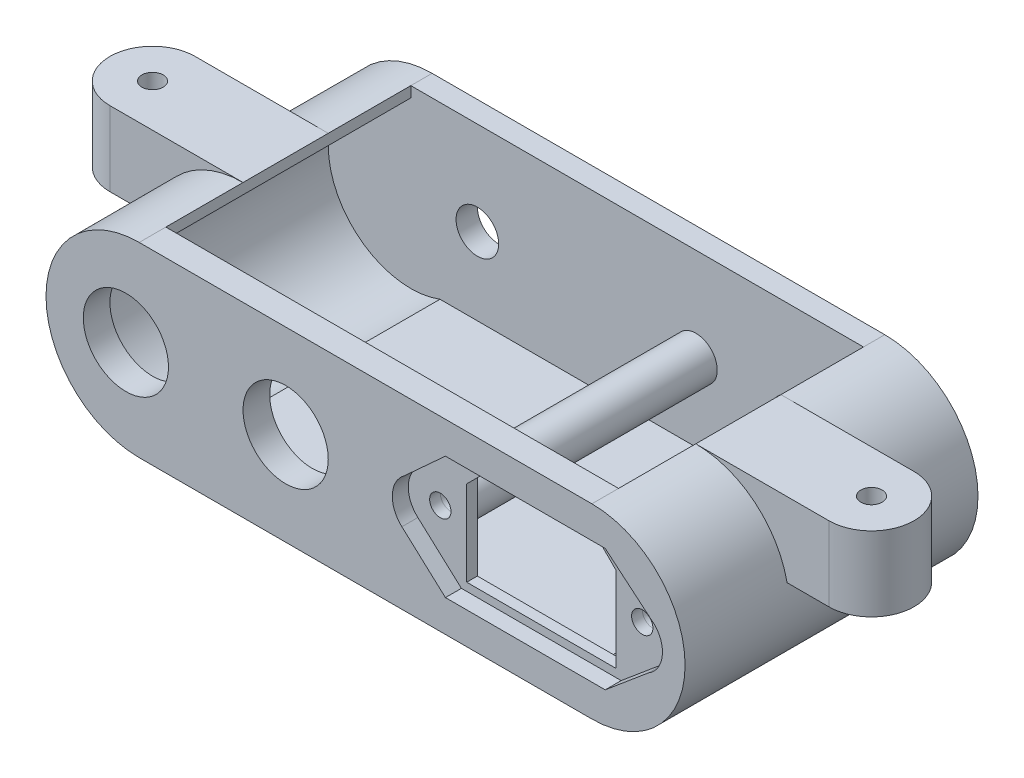
SolidWorks part; units mm, degrees
ref_plane "Front Plane" through (0, 0, 0) normal (0, 0, 1) x (1, 0, 0)
ref_plane "Top Plane" through (0, 0, 0) normal (0, 1, 0) x (1, 0, 0)
ref_plane "Right Plane" through (0, 0, 0) normal (1, 0, 0) x (0, 0, -1)
sketch "Sketch1" plane through (0, 0, 0) normal (0, 0, 1) x (1, 0, 0)
  line L1 (-60, 17.5) -> (60, 17.5)
  line L2 (-60, 17.5) -> (-60, -17.5)
  line L3 (-60, -17.5) -> (60, -17.5)
  line L4 (60, 17.5) -> (60, -17.5)
  line L5 (-60, 17.5) -> (60, -17.5) construction
  line L6 (-60, -17.5) -> (60, 17.5) construction
  point P0 (0, 0)
  dimension "D1" = 120
  dimension "D2" = 35
extrude "Boss-Extrude1" add sketch "Sketch1" along normal blind 5
sketch "Sketch2" plane through (0, 0, 5) normal (0, 0, 1) x (1, 0, 0)
  line L0 (0, 0) -> (60, 0) construction
  line L2 (60, -17.5) -> (60, 17.5) construction
  line L3 (0, 17.5) -> (0, -17.5) construction
  line L4 (60, 17.5) -> (-60, 17.5) construction
  line L5 (-60, -17.5) -> (60, -17.5) construction
  line L6 (30, 17.5) -> (30, -17.5) construction
  line L7 (0, 11.5) -> (60, 11.5) construction
  line L8 (0, -11.5) -> (60, -11.5) construction
  line L9 (55, 11.5) -> (55, -11.5) construction
  line L10 (5, 11.5) -> (5, -11.5) construction
  point P20 (5, 0)
  dimension "D1" = 5
  dimension "D2" = 5
  dimension "D3" = 23
sketch "Sketch3" plane through (0, 0, 5) normal (0, 0, 1) x (1, 0, 0)
  line L0 (50.6107, -240.2548) -> (338.3067, -263.9078) construction
sketch "Sketch4" plane through (0, 0, 5) normal (0, 0, 1) x (1, 0, 0)
  line L0 (0, 0) -> (60, 0) construction
  line L1 (15, -11.5) -> (45, -11.5)
  line L3 (15, 11.5) -> (45, 11.5)
  line L7 (0, 11.5) -> (60, 11.5) construction
  line L8 (15, 11.5) -> (7.2913, 4.4518)
  line L9 (15, -11.5) -> (6.8227, -4.0709)
  line L10 (45, 11.5) -> (54.4001, 3.6146)
  line L11 (45, -11.5) -> (53.0932, -4.7109)
  arc A0 (7.2913, 4.4518) -> (6.8227, -4.0709) centre (10.5211, 0) ccw
  arc A3 (53.0932, -4.7109) -> (54.4001, 3.6146) centre (50.2547, 0) ccw
  point P0 (30, 0)
  dimension "D2" = 11
  dimension "D1" = 30
extrude "Cut-Extrude1" cut sketch "Sketch4" against normal blind 3
sketch "Sketch5" plane through (0, 0, 2) normal (0, 0, 1) x (1, 0, 0)
  line L0 (0, 0) -> (60, 0) construction
  line L1 (16, 10) -> (44, 10)
  line L2 (16, 10) -> (16, -10)
  line L3 (16, -10) -> (44, -10)
  line L4 (44, 10) -> (44, -10)
  line L5 (16, 10) -> (44, -10) construction
  line L6 (16, -10) -> (44, 10) construction
  point P0 (30, 0)
  dimension "D1" = 28
  dimension "D2" = 20
extrude "Cut-Extrude2" cut sketch "Sketch5" against normal blind 3
chamfer "Chamfer1" distance 4 angle 45 2 edges at (44, 10, 1) (16, 10, 1)
sketch "Sketch6" plane through (0, 0, 5) normal (0, 0, 1) x (1, 0, 0)
  line L0 (0, 17.5) -> (0, -17.5) construction
  line L1 (60, 17.5) -> (-60, 17.5) construction
  line L2 (-60, -17.5) -> (60, -17.5) construction
  line L3 (-45, 0) -> (-30, 0) construction
  line L5 (-30, 17.5) -> (-30, -17.5) construction
  line L6 (-15, 0) -> (-30, 0) construction
  line L7 (-30, 17.5) -> (-60, 17.5) construction
  line L8 (-60, 17.5) -> (-60, -17.5) construction
  line L9 (-45, 17.5) -> (-45, -17.5) construction
  circle A0 centre (-15, 0) radius 8
  circle A1 centre (-45, 0) radius 8
  dimension "D1" = 16
  dimension "D2" = 16
extrude "Cut-Extrude3" cut sketch "Sketch6" against normal blind 5
sketch "Sketch7" plane through (0, 0, 2) normal (0, 0, 1) x (1, 0, 0)
  line L0 (30, 17.5) -> (30, -17.5) construction
  circle A0 centre (11.0381, 0) radius 2
  circle A1 centre (48.9619, 0) radius 2
  dimension "D1" = 4
extrude "Cut-Extrude4" cut sketch "Sketch7" against normal blind 5
sketch "Sketch8" plane through (0, 0, 5) normal (0, 0, 1) x (1, 0, 0)
  line L1 (60, -17.5) -> (42.5, -17.5)
  line L2 (60, -17.5) -> (60, 17.5)
  line L3 (60, 17.5) -> (42.5, 17.5)
  line L4 (-60, -17.5) -> (-60, 17.5)
  line L7 (-42.5, 17.5) -> (-60, 17.5)
  line L8 (-42.5, -17.5) -> (-60, -17.5)
  arc A0 (-42.5, 17.5) -> (-42.5, -17.5) centre (-42.5, 0) ccw
  arc A1 (42.5, -17.5) -> (42.5, 17.5) centre (42.5, 0) ccw
  point P0 (0, 0)
  line M16 (60, -17.5) -> (60, 17.5)
  line M17 (60, 17.5) -> (-60, 17.5)
  line M18 (-60, 17.5) -> (-60, -17.5)
  line M19 (-60, -17.5) -> (60, -17.5)
  dimension "D1" = 35
extrude "Cut-Extrude5" cut sketch "Sketch8" against normal blind 5 contours A0 M17 M18 | A0 L4 M19 | A1 L2 M17 | A1 M19 M16
sketch "Sketch9" plane through (0, 0, 0) normal (0, 0, -1) x (-1, 0, 0)
  line L0 (-42.5, 17.5) -> (-42.5, -17.5) construction
  line L1 (42.5, 17.5) -> (42.5, -17.5) construction
  line L3 (-42.5, -17.5) -> (42.5, -17.5)
  line L4 (-42.5, -17.5) -> (-42.5, -14.5)
  line L5 (-42.5, -14.5) -> (42.5, -14.5)
  line L6 (42.5, -17.5) -> (42.5, -14.5)
  dimension "D1" = 3
extrude "Boss-Extrude2" add sketch "Sketch9" along normal blind 50
sketch "Sketch10" plane through (0, -14.5, 0) normal (0, 1, 0) x (1, 0, 0)
  line L0 (42.5, 50) -> (42.5, 0) construction
  line L1 (-42.5, 50) -> (42.5, 50)
  line L2 (-42.5, 50) -> (-42.5, 46)
  line L3 (-42.5, 46) -> (42.5, 46)
  line L4 (42.5, 50) -> (42.5, 46)
  dimension "D1" = 4
extrude "Boss-Extrude3" add sketch "Sketch10" along normal up to surface (32 mm away) up to face at (0, 17.5, 2.5)
sketch "Sketch11" plane through (0, 0, 0) normal (0, 0, -1) x (-1, 0, 0)
  line L0 (-42.5, 17.5) -> (-42.5, -17.5) construction
  line L1 (42.5, -17.5) -> (42.5, 17.5) construction
  line L2 (42.5, 17.5) -> (42.5, 15.5)
  line L3 (-42.5, 17.5) -> (-42.5, 15.5)
  line L4 (-42.5, -15.5) -> (-42.5, -17.5)
  line L5 (42.5, -15.5) -> (42.5, -17.5)
  arc A0 (-42.5, 17.5) -> (-42.5, -17.5) centre (-42.5, 0) ccw
  arc A1 (-42.5, 15.5) -> (-42.5, -15.5) centre (-42.5, 0) ccw
  arc A2 (42.5, -17.5) -> (42.5, 17.5) centre (42.5, 0) ccw
  arc A3 (42.5, -15.5) -> (42.5, 15.5) centre (42.5, 0) ccw
  dimension "D1" = 2
extrude "Boss-Extrude4" add sketch "Sketch11" along normal up to surface (50 mm away) up to face at (0, 0, -50)
sketch "Sketch12" plane through (0, 0, -50) normal (0, 0, -1) x (-1, 0, 0)
  line L0 (42.5, -15.5) -> (42.5, 15.5) construction
  circle A0 centre (-42.5, 0) radius 17.5
  circle A1 centre (42.5, 0) radius 17.5
extrude "Boss-Extrude5" add sketch "Sketch12" against normal up to surface (4 mm away) up to face at (0, 6.1667, -46)
sketch "Sketch13" plane through (0, 0, -50) normal (0, 0, -1) x (-1, 0, 0)
  line L0 (-30, 10) -> (-30, -11.5) construction
  line L1 (-40, 10) -> (-20, 10) construction
  line L2 (-15, -11.5) -> (-45, -11.5) construction
  line L3 (-44, -2) -> (-16, -2) construction
  line L4 (-44, -10) -> (-44, 6) construction
  line L5 (-16, 6) -> (-16, -10) construction
  line L6 (7, 0) -> (53, 0) construction
  circle A0 centre (-30, -2) radius 5
  circle A1 centre (15, 0) radius 8 construction
  circle A2 centre (45, 0) radius 8 construction
  circle A3 centre (30, 0) radius 4
  dimension "D1" = 8
  dimension "D2" = 10
extrude "Cut-Extrude6" cut sketch "Sketch13" against normal up to surface (4 mm away) up to face at (0, 0.75, -46)
sketch "Sketch14" plane through (0, 17.5, 0) normal (0, 1, 0) x (1, 0, 0)
  line L0 (0, 50) -> (0, -5) construction
  line L1 (-42.5, 50) -> (42.5, 50) construction
  line L2 (42.5, -5) -> (-42.5, -5) construction
  line L3 (0, 22.5) -> (-42.5, 22.5) construction
  line L4 (-42.5, 46) -> (-42.5, 0) construction
  line L5 (0, 22.5) -> (42.5, 22.5) construction
  line L6 (42.5, 46) -> (42.5, 0) construction
  line L7 (-42.5, 22.5) -> (-67.5, 22.5) construction
  line L8 (-42.5, 14.5) -> (-67.5, 14.5)
  line L9 (-42.5, 30.5) -> (-67.5, 30.5)
  line L10 (-42.5, 30.5) -> (-42.5, 14.5)
  line L11 (42.5, 30.5) -> (67.5, 30.5)
  line L12 (42.5, 30.5) -> (42.5, 14.5)
  line L13 (42.5, 14.5) -> (67.5, 14.5)
  arc A1 (-67.5, 30.5) -> (-67.5, 14.5) centre (-67.5, 22.5) ccw
  arc A2 (67.5, 30.5) -> (67.5, 14.5) centre (67.5, 22.5) cw
  point P10 (-55, 22.5)
  dimension "D2" = 8
  dimension "D1" = 25
extrude "Boss-Extrude6" add sketch "Sketch14" against normal blind 14
sketch "Sketch15" plane through (0, 0, 0) normal (0, 0, -1) x (-1, 0, 0)
  circle A0 centre (-42.5, 0) radius 15.5
  circle A1 centre (42.5, 0) radius 15.5
extrude "Cut-Extrude7" cut sketch "Sketch15" along normal up to surface (46 mm away) up to face at (25, -2, -46)
sketch "Sketch16" plane through (0, 3.5, 0) normal (0, -1, 0) x (1, 0, 0)
  circle A0 centre (67.5, -22.5) radius 3.5
  circle A1 centre (-67.5, -22.5) radius 3.5
  dimension "D1" = 7
extrude "Cut-Extrude8" cut sketch "Sketch16" against normal blind 2
sketch "Sketch17" plane through (0, 3.5, 0) normal (0, -1, 0) x (1, 0, 0)
  circle A0 centre (-67.5, -22.5) radius 2
  circle A1 centre (67.5, -22.5) radius 2
  dimension "D1" = 4
extrude "Cut-Extrude9" cut sketch "Sketch17" against normal through all
sketch "Sketch18" plane through (0, 0, 0) normal (0, 0, -1) x (-1, 0, 0)
  circle A0 centre (-48.9619, 0) radius 4
  circle A1 centre (-11.0381, 0) radius 4
  dimension "D1" = 8
extrude "Boss-Extrude7" add sketch "Sketch18" along normal through all
sketch "Sketch19" plane through (0, 0, 0) normal (0, 0, 1) x (1, 0, 0)
  line L0 (30, 10) -> (30, -10) construction
  line L1 (40, 10) -> (20, 10) construction
  line L2 (16, -10) -> (44, -10) construction
  circle A0 centre (11.0381, 0) radius 2
  circle A1 centre (48.9619, 0) radius 2
  dimension "D1" = 4
extrude "Cut-Extrude10" cut sketch "Sketch19" against normal blind 20 draft 3
